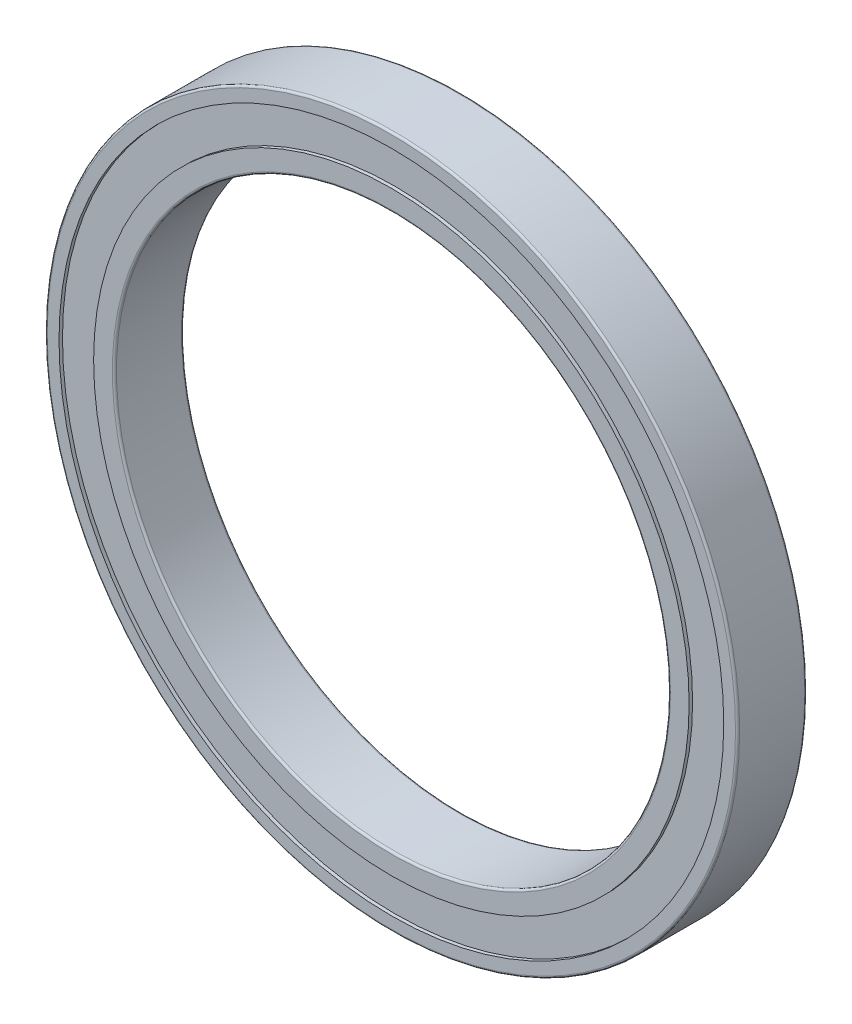
SolidWorks part; units mm, degrees
material "Acier non allié"
ref_plane "Plan de face" through (0, 0, 0) normal (0, 0, 1) x (1, 0, 0)
ref_plane "Plan de dessus" through (0, 0, 0) normal (0, 1, 0) x (1, 0, 0)
ref_plane "Plan de droite" through (0, 0, 0) normal (1, 0, 0) x (0, 0, -1)
sketch "Esquisse1" plane through (0, 0, 0) normal (0, 0, 1) x (1, 0, 0)
  circle A0 centre (0, 0) radius 40
  circle A1 centre (0, 0) radius 50
  dimension "D1" = 80
  dimension "D2" = 100
extrude "Boss.-Extru.1" add sketch "Esquisse1" along normal blind 10
sketch "Esquisse2" plane through (0, 0, 10) normal (0, 0, 1) x (1, 0, 0)
  circle A0 centre (0, 0) radius 48
  circle A1 centre (0, 0) radius 43
  circle A2 centre (0, 0) radius 50 construction
  circle A3 centre (0, 0) radius 40 construction
  dimension "D1" = 2
  dimension "D2" = 3
extrude "Enlèv. mat.-Extru.1" cut sketch "Esquisse2" against normal blind 0.5
sketch "Esquisse3" plane through (0, 0, 0) normal (0, 0, -1) x (-1, 0, 0)
  circle A1 centre (0, 0) radius 43
  circle A2 centre (0, 0) radius 43
  circle A3 centre (0, 0) radius 48
  circle A4 centre (0, 0) radius 48
  dimension "D1" = 0
  dimension "D2" = 0
extrude "Enlèv. mat.-Extru.2" cut sketch "Esquisse3" against normal blind 0.5
fillet "Congé1" radius 0.3 4 edges at (40, 0, 0) (40, 0, 10) (50, 0, 0) (50, 0, 10)
